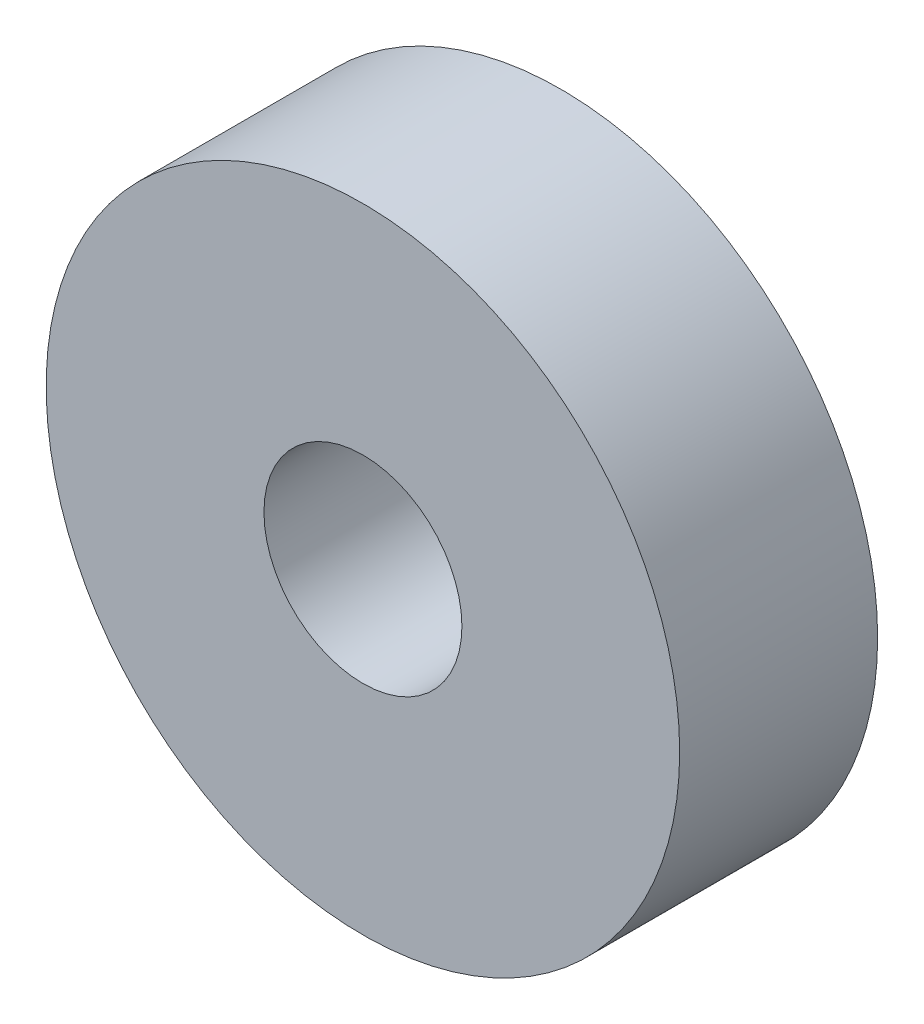
SolidWorks part; units mm, degrees
ref_plane "Alzado" through (0, 0, 0) normal (0, 0, 1) x (1, 0, 0)
ref_plane "Planta" through (0, 0, 0) normal (0, 1, 0) x (1, 0, 0)
ref_plane "Vista lateral" through (0, 0, 0) normal (1, 0, 0) x (0, 0, -1)
sketch "Croquis1" plane through (0, 0, 0) normal (0, 0, 1) x (1, 0, 0)
  circle A0 centre (0, 0) radius 2.5
  circle A1 centre (0, 0) radius 8
  dimension "D1" = 16
  dimension "D2" = 5
extrude "Saliente-Extruir1" add sketch "Croquis1" along normal blind 5
